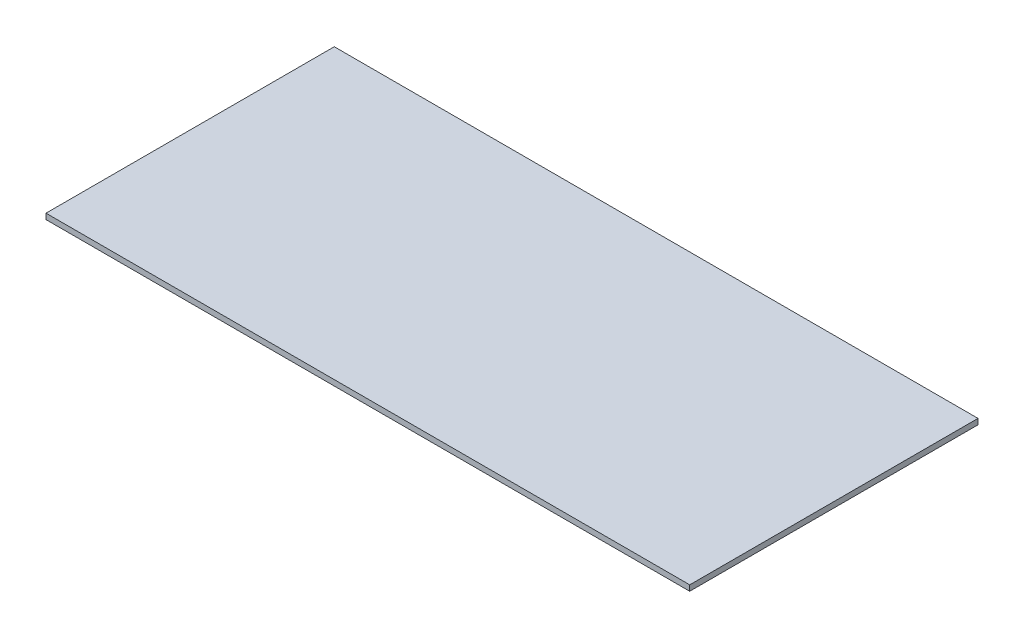
SolidWorks part; units mm, degrees
ref_plane "Front Plane" through (0, 0, 0) normal (0, 0, 1) x (1, 0, 0)
ref_plane "Top Plane" through (0, 0, 0) normal (0, 1, 0) x (1, 0, 0)
ref_plane "Right Plane" through (0, 0, 0) normal (1, 0, 0) x (0, 0, -1)
sketch "Sketch1" plane through (0, 0, 0) normal (0, 1, 0) x (1, 0, 0)
  line L1 (115, -51.5) -> (-115, -51.5)
  line L2 (115, -51.5) -> (115, 51.5)
  line L3 (115, 51.5) -> (-115, 51.5)
  line L4 (-115, -51.5) -> (-115, 51.5)
  line L5 (115, -51.5) -> (-115, 51.5) construction
  line L6 (115, 51.5) -> (-115, -51.5) construction
  point P0 (0, 0)
  dimension "D1" = 103
  dimension "D2" = 230
extrude "Boss-Extrude1" add sketch "Sketch1" along normal blind 2
